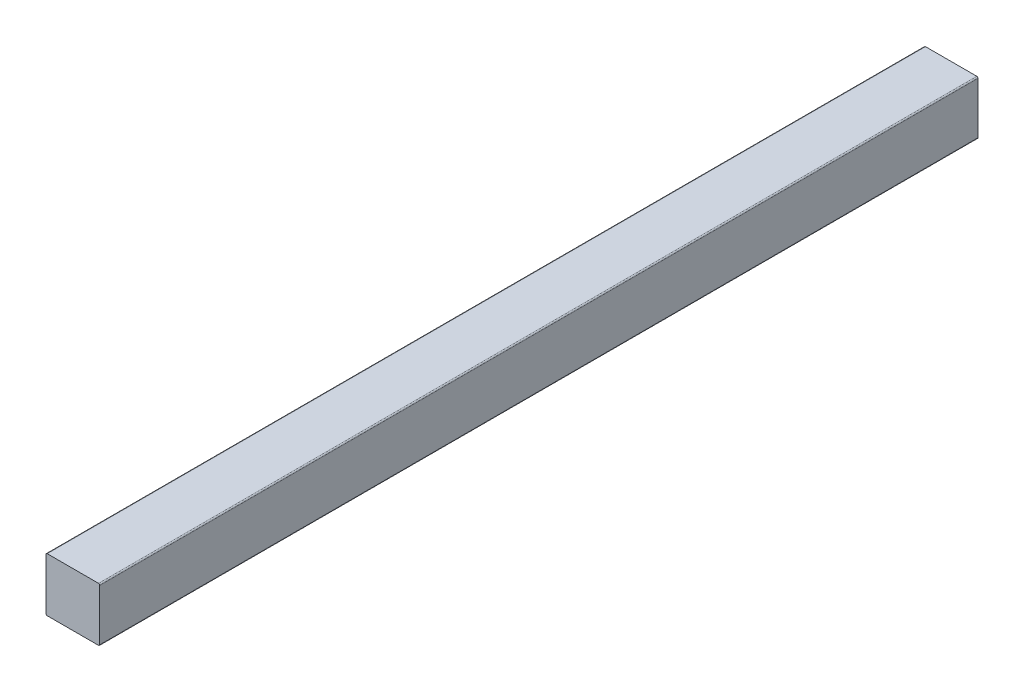
SolidWorks part; units mm, degrees
ref_plane "Front Plane" through (0, 0, 0) normal (0, 0, 1) x (1, 0, 0)
ref_plane "Top Plane" through (0, 0, 0) normal (0, 1, 0) x (1, 0, 0)
ref_plane "Right Plane" through (0, 0, 0) normal (1, 0, 0) x (0, 0, -1)
sketch "Sketch1" plane through (0, 0, 0) normal (0, 0, 1) x (1, 0, 0)
  line L0 (33.5, -34) -> (2.5, -34) construction
  line L1 (1, 10) -> (45, 10)
  line L2 (1, 10) -> (1, -34)
  line L3 (1, -34) -> (45, -34)
  line L4 (45, 10) -> (45, -34)
  line L5 (45, 806) -> (45, -84) construction
  line L6 (1, -84) -> (1, 806) construction
extrude "Boss-Extrude1" add sketch "Sketch1" along normal blind 719
fillet "Fillet2" [suppressed] radius 1
fillet "Fillet3" radius 1 4 edges at (1, -34, 359.5) (45, -34, 359.5) (1, 10, 359.5) (45, 10, 359.5)
